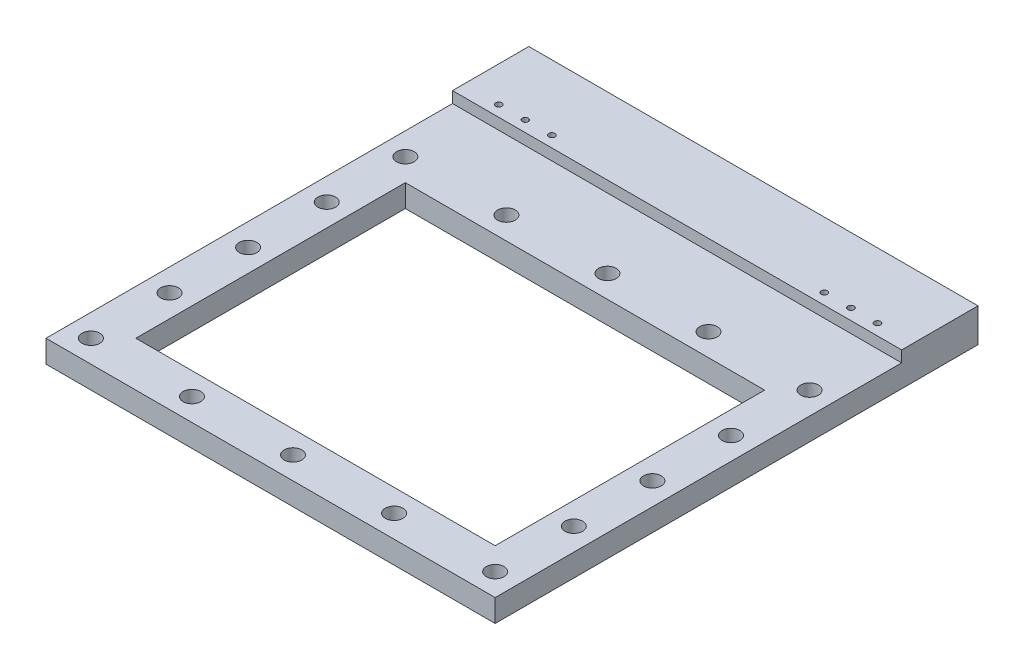
SolidWorks part; units mm, degrees
ref_plane "Front Plane" through (0, 0, 0) normal (0, 0, 1) x (1, 0, 0)
ref_plane "Top Plane" through (0, 0, 0) normal (0, 1, 0) x (1, 0, 0)
ref_plane "Right Plane" through (0, 0, 0) normal (1, 0, 0) x (0, 0, -1)
sketch "Sketch1" plane through (0, 0, 0) normal (0, 1, 0) x (1, 0, 0)
  line L1 (0, 0) -> (254, 0)
  line L2 (0, 0) -> (0, 203.2)
  line L3 (0, 203.2) -> (254, 203.2)
  line L4 (254, 0) -> (254, 203.2)
  line L5 (12.7, 190.5) -> (241.3, 190.5) construction
  line L6 (12.7, 190.5) -> (12.7, 12.7) construction
  line L7 (25.4, 177.8) -> (228.6, 177.8)
  line L8 (25.4, 177.8) -> (25.4, 25.4)
  line L9 (25.4, 25.4) -> (228.6, 25.4)
  line L10 (228.6, 177.8) -> (228.6, 25.4)
  line L11 (12.7, 12.7) -> (241.3, 12.7) construction
  line L12 (241.3, 190.5) -> (241.3, 12.7) construction
  circle A0 centre (12.7, 190.5) radius 3.05
  circle A1 centre (241.3, 190.5) radius 3.05
  circle A2 centre (241.3, 12.7) radius 3.05
  circle A3 centre (12.7, 12.7) radius 3.05
  dimension "D11" = 6.1
  dimension "D12" = 6.1
  dimension "D13" = 6.1
  dimension "D14" = 6.1
  dimension "D1" = 254
  dimension "D2" = 203.2
  dimension "D3" = 25.4
  dimension "D4" = 25.4
  dimension "D5" = 25.4
  dimension "D6" = 25.4
  dimension "D7" = 12.7
  dimension "D8" = 12.7
  dimension "D9" = 12.7
  dimension "D10" = 12.7
extrude "Boss-Extrude1" add sketch "Sketch1" along normal blind 12.7
sketch "Sketch5" plane through (0, 0, 0) normal (0, -1, 0) x (1, 0, 0)
  line L1 (254, -203.2) -> (0, -203.2)
  line L2 (254, -203.2) -> (254, -222.25)
  line L3 (254, -222.25) -> (0, -222.25)
  line L4 (0, -203.2) -> (0, -222.25)
  dimension "D1" = 19.05
extrude "Boss-Extrude3" add sketch "Sketch5" against normal blind 12.7
sketch "Sketch6" plane through (0, 12.7, 0) normal (0, 1, 0) x (1, 0, 0)
  line L0 (0, 222.25) -> (254, 222.25) construction
  line L1 (12.7, 222.25) -> (57.15, 222.25) construction
  line L2 (12.7, 222.25) -> (12.7, 209.55) construction
  line L3 (12.7, 209.55) -> (57.15, 209.55) construction
  line L4 (57.15, 222.25) -> (57.15, 209.55) construction
  line L5 (12.925, 223.1204) -> (50012.925, 223.1204) construction
  line L10 (0, 222.25) -> (0, 0) construction
  line L12 (12.925, 210.1204) -> (56.925, 210.1204) construction
  line L13 (12.925, 210.1204) -> (12.925, 242.1204) construction
  line L14 (12.925, 242.1204) -> (56.925, 242.1204) construction
  line L15 (56.925, 210.1204) -> (56.925, 242.1204) construction
  line L19 (127, 222.25) -> (127, -49777.75) construction
  line L20 (228.6, 177.8) -> (25.4, 177.8) construction
  line L21 (12.925, 216.1204) -> (50012.925, 216.1204) construction
  line L22 (34.925, 242.1204) -> (34.925, -49757.8796) construction
  line L23 (49.925, 242.1204) -> (49.925, -49757.8796) construction
  line L24 (19.925, 242.1204) -> (19.925, -49757.8796) construction
  line L25 (197.075, 210.1204) -> (197.075, 242.1204) construction
  line L26 (241.075, 242.1204) -> (197.075, 242.1204) construction
  line L27 (241.075, 210.1204) -> (241.075, 242.1204) construction
  line L28 (241.075, 210.1204) -> (197.075, 210.1204) construction
  line L29 (196.85, 222.25) -> (196.85, 209.55) construction
  line L30 (241.3, 209.55) -> (196.85, 209.55) construction
  line L31 (241.3, 222.25) -> (241.3, 209.55) construction
  line L32 (241.3, 222.25) -> (196.85, 222.25) construction
  line L33 (12.925, 236.1204) -> (50012.925, 236.1204) construction
  line L34 (12.925, 229.1204) -> (50012.925, 229.1204) construction
  line L35 (219.075, 216.1204) -> (219.075, 50216.1204) construction
  line L36 (234.075, 216.1204) -> (234.075, 50216.1204) construction
  line L37 (204.0632, 216.1204) -> (204.0632, 50216.1204) construction
  circle A0 centre (19.925, 216.1204) radius 2
  circle A1 centre (34.925, 216.1204) radius 2
  circle A2 centre (49.9368, 216.1204) radius 2
  circle A3 centre (204.0632, 216.1204) radius 2
  circle A4 centre (219.075, 216.1204) radius 2
  circle A5 centre (234.075, 216.1204) radius 2
  point P10 (56.925, 226.1204)
  point P24 (127, 222.25)
  point P27 (127, 177.8)
  point P29 (34.925, 242.1204)
  point P30 (34.925, 210.1204)
  point P62 (219.075, 242.1204)
  dimension "D11" = 4
  dimension "D12" = 4
  dimension "D13" = 4
  dimension "D1" = 44.45
  dimension "D2" = 13
  dimension "D3" = 10
  dimension "D4" = 12.7
  dimension "D5" = 12.7
  dimension "D6" = 15
  dimension "D7" = 32
  dimension "D8" = 44
  dimension "D9" = 0.225
  dimension "D10" = 15
  dimension "D14" = 20
  dimension "D15" = 13
extrude "Cut-Extrude2" cut sketch "Sketch6" against normal blind 4.5
sketch "Sketch7" plane through (0, 8.2, 0) normal (0, 1, 0) x (1, 0, 0)
  circle A0 centre (19.925, 216.1204) radius 1.75
  circle A1 centre (34.925, 216.1204) radius 1.75
  circle A2 centre (49.9368, 216.1204) radius 1.75
  circle A3 centre (204.0632, 216.1204) radius 1.75
  circle A4 centre (219.075, 216.1204) radius 1.75
  circle A5 centre (234.075, 216.1204) radius 1.75
  dimension "D1" = 3.5
  dimension "D2" = 3.5
  dimension "D3" = 3.5
  dimension "D4" = 3.5
  dimension "D5" = 3.5
  dimension "D6" = 3.5
extrude "Cut-Extrude3" cut sketch "Sketch7" against normal blind 4.5
sketch "Sketch8" plane through (0, 12.7, 0) normal (0, 1, 0) x (1, 0, 0)
  line L0 (19.925, 216.1204) -> (50019.925, 216.1204) construction
  line L1 (0, 222.25) -> (13.1503, 222.25)
  line L2 (0, 222.25) -> (0, 273.05)
  line L3 (0, 273.05) -> (254, 273.05)
  line L4 (254, 222.25) -> (254, 273.05)
  line L5 (-9.9034, 236.1204) -> (49990.0966, 236.1204) construction
  line L6 (243.6521, 222.25) -> (254, 222.25)
  line L8 (13.1503, 222.25) -> (13.1503, 209.3543)
  line L9 (13.1503, 209.3543) -> (243.6521, 209.3543)
  line L10 (243.6521, 222.25) -> (243.6521, 209.3543)
  line L11 (19.925, 216.1204) -> (19.925, 50216.1204) construction
  line L12 (34.925, 216.1204) -> (34.925, 50216.1204) construction
  line L13 (49.9368, 216.1204) -> (49.9368, 50216.1204) construction
  line L14 (204.0632, 216.1204) -> (204.0632, 50216.1204) construction
  line L15 (219.075, 216.1204) -> (219.075, 50216.1204) construction
  line L16 (234.075, 216.1204) -> (234.075, 50216.1204) construction
  line L17 (202.3132, 216.1204) -> (202.3132, 50216.1204) construction
  line L18 (217.325, 216.1204) -> (217.325, 50216.1204) construction
  line L19 (232.325, 216.1204) -> (232.325, 50216.1204) construction
  line L20 (18.175, 216.1204) -> (18.175, 50216.1204) construction
  line L21 (33.175, 216.1204) -> (33.175, 50216.1204) construction
  line L22 (48.1868, 216.1204) -> (48.1868, 50216.1204) construction
  line L24 (5.2825, 194.3203) -> (19.925, 194.3203)
  line L25 (5.2825, 194.3203) -> (5.2825, 184.9665)
  line L26 (5.2825, 184.9665) -> (19.925, 184.9665)
  line L27 (19.925, 194.3203) -> (19.925, 184.9665)
  line L28 (231.031, 194.3203) -> (247.2991, 194.3203)
  line L29 (231.031, 194.3203) -> (231.031, 184.9665)
  line L30 (231.031, 184.9665) -> (247.2991, 184.9665)
  line L31 (247.2991, 194.3203) -> (247.2991, 184.9665)
  line L32 (234.075, 17.5721) -> (247.2991, 17.5721)
  line L33 (234.075, 17.5721) -> (234.075, 7.1611)
  line L34 (234.075, 7.1611) -> (247.2991, 7.1611)
  line L35 (247.2991, 17.5721) -> (247.2991, 7.1611)
  line L36 (5.2825, 17.5721) -> (19.925, 17.5721)
  line L37 (5.2825, 17.5721) -> (5.2825, 7.1611)
  line L38 (5.2825, 7.1611) -> (19.925, 7.1611)
  line L39 (19.925, 17.5721) -> (19.925, 7.1611)
  circle A16 centre (49.9368, 236.1204) radius 1.75
  circle A17 centre (34.925, 236.1204) radius 1.75
  circle A18 centre (19.925, 236.1204) radius 1.75
  circle A19 centre (204.0632, 236.1204) radius 1.75
  circle A20 centre (219.075, 236.1204) radius 1.75
  circle A21 centre (234.075, 236.1204) radius 1.75
  dimension "D1" = 50.8
  dimension "D2" = 20
extrude "Boss-Extrude4" add sketch "Sketch8" against normal blind 12.7
sketch "Sketch9" plane through (0, 12.7, 0) normal (0, 1, 0) x (1, 0, 0)
  line L0 (254, 0) -> (254, 273.05) construction
  line L1 (0, 273.05) -> (254, 273.05)
  line L2 (0, 273.05) -> (0, 229.87)
  line L3 (0, 229.87) -> (254, 229.87)
  line L4 (254, 273.05) -> (254, 229.87)
  line L5 (0, 226.1204) -> (50000, 226.1204) construction
  line L7 (0, 229.1204) -> (50000, 229.1204) construction
  line L9 (254, 242.1204) -> (-49746, 242.1204) construction
  circle A0 centre (19.925, 236.1204) radius 1.75
  circle A1 centre (34.925, 236.1204) radius 1.7074
  circle A2 centre (49.9368, 236.1204) radius 1.75
  circle A3 centre (204.0632, 236.1204) radius 1.75
  circle A4 centre (219.075, 236.1204) radius 1.75
  circle A5 centre (234.075, 236.1204) radius 1.75
  dimension "D1" = 10
  dimension "D2" = 43.18
  dimension "D3" = 16
  dimension "D4" = 13
extrude "Boss-Extrude5" add sketch "Sketch9" along normal blind 6.35
hole_wizard "CBORE for M5 SHCS2" positions "Sketch10" profile "Sketch11" counterbore size "M5" standard "ANSI Metric" end condition through all
sketch "Sketch10" plane through (0, 12.7, 0) normal (0, 1, 0) x (1, 0, 0)
  line L0 (127, 177.8) -> (127, -49822.2) construction
  line L1 (228.6, 177.8) -> (25.4, 177.8) construction
  line L2 (25.4, 25.4) -> (228.6, 25.4) construction
  line L3 (241.3, 190.5) -> (241.3, -49809.5) construction
  line L4 (12.7, 190.6173) -> (12.7, -49809.3827) construction
  line L5 (241.6666, 190.5) -> (-49758.3334, 190.5) construction
  line L6 (241.6666, 12.7) -> (-49758.3334, 12.7) construction
  line L8 (0, 0) -> (254, 0) construction
  line L9 (228.6, 25.4) -> (228.6, 177.8) construction
  line L10 (25.4, 177.8) -> (25.4, 25.4) construction
  line L11 (184.15, 190.5) -> (184.15, -49809.5) construction
  line L12 (69.85, 190.5) -> (69.85, -49809.5) construction
  line L13 (228.6, 101.6) -> (-49771.4, 101.6) construction
  line L14 (241.3, 57.15) -> (-49758.7, 57.15) construction
  line L15 (241.3, 146.05) -> (-49758.7, 146.05) construction
  point P33 (127, 177.8)
  point P36 (127, 25.4)
  point P68 (241.3, 190.5)
  point P70 (12.7, 12.7)
  point P72 (12.7, 190.5)
  point P74 (127, 190.5)
  point P76 (127, 12.7)
  point P78 (241.3, 12.7)
  point P88 (228.6, 101.6)
  point P89 (25.4, 101.6)
  point P96 (184.15, 190.5)
  point P98 (184.15, 12.7)
  point P100 (69.85, 12.7)
  point P102 (69.85, 190.5)
  point P104 (12.7, 146.05)
  point P106 (12.7, 57.15)
  point P108 (241.3, 57.15)
  point P110 (241.3, 146.05)
  point P112 (241.3, 101.6)
  point P114 (12.7, 101.6)
  dimension "D1" = 12.7
  dimension "D2" = 12.7
  dimension "D3" = 12.7
  dimension "D4" = 12.7
  dimension "D5" = 114.3
  dimension "D6" = 57.15
  dimension "D7" = 57.15
  dimension "D8" = 88.9
  dimension "D9" = 44.45
  dimension "D10" = 44.45
sketch "Sketch11" plane through (12.7, 12.7, -101.6) normal (1, 0, 0) x (0, 0, 1)
  line L0 (0, 0) -> (0, 12.7)
  line L1 (0, 12.7) -> (2.9, 12.7)
  line L3 (2.9, 12.7) -> (2.9, 8)
  line L4 (2.9, 8) -> (5, 8)
  line L5 (5, 8) -> (5, 0)
  line L7 (5, 0) -> (0, 0)
  line L11 (0, -6.35) -> (0, 107.95) construction
  dimension "Thru Hole Dia." = 5.8
  dimension "Thru Hole Depth" = 12.7
  dimension "C'Bore Dia." = 10
  dimension "C'Bore Depth" = 8
sketch "Sketch12" plane through (0, 0, 0) normal (0, -1, 0) x (1, 0, 0)
  line L0 (19.925, -236.1204) -> (50019.925, -236.1204) construction
  line L1 (19.925, -236.1204) -> (19.925, 49763.8796) construction
  line L2 (34.925, -236.1204) -> (34.925, 49763.8796) construction
  line L3 (49.9368, -236.1204) -> (49.9368, 49763.8796) construction
  line L4 (204.0632, -236.1204) -> (204.0632, 49763.8796) construction
  line L5 (219.075, -236.1204) -> (219.075, 49763.8796) construction
  line L6 (234.075, -236.1204) -> (234.075, 49763.8796) construction
  circle A0 centre (219.075, -236.1204) radius 2
  circle A1 centre (204.0632, -236.1204) radius 2
  circle A2 centre (49.9368, -236.1204) radius 2
  circle A3 centre (34.925, -236.1204) radius 2
  circle A4 centre (19.925, -236.1204) radius 2
  circle A7 centre (234.075, -236.1204) radius 2
  dimension "D1" = 4
  dimension "D2" = 4
  dimension "D3" = 4
  dimension "D4" = 4
  dimension "D5" = 4
  dimension "D6" = 4
extrude "Cut-Extrude4" cut sketch "Sketch12" against normal blind 11
